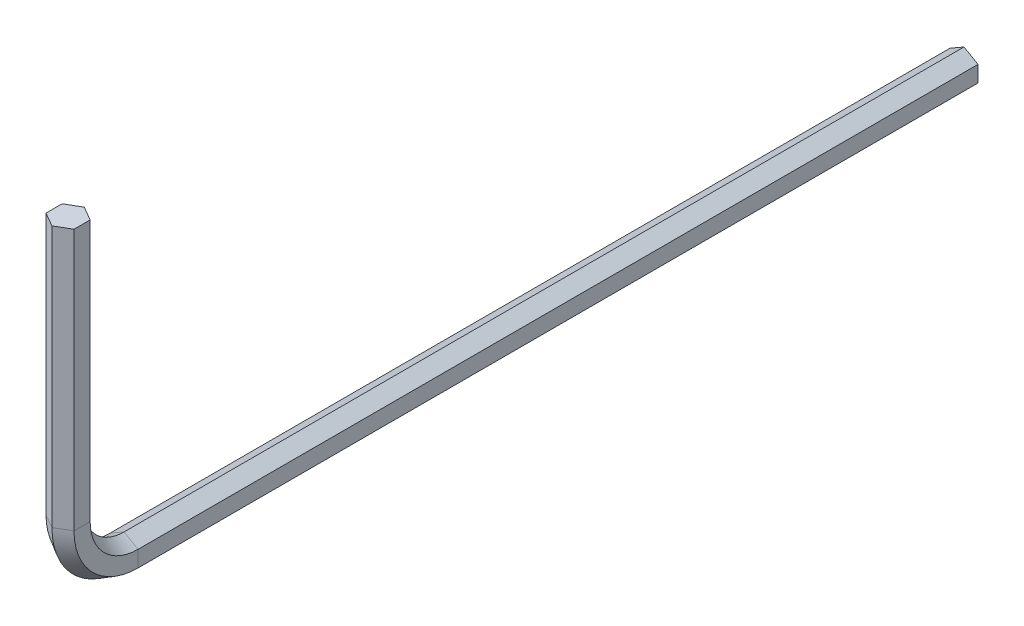
SolidWorks part; units mm, degrees
ref_plane "Front Plane" through (0, 0, 0) normal (1, 0, 0) x (0, 1, 0)
ref_plane "Top Plane" through (0, 0, 0) normal (0, 0, 1) x (0, 1, 0)
ref_plane "Right Plane" through (0, 0, 0) normal (0, 1, 0) x (-1, 0, 0)
sketch "Sketch1" plane through (0, 0, 0) normal (0, 0, 1) x (0, 1, 0)
  line L2 (0.866, 0) -> (0.433, 0.75)
  line L3 (0.433, 0.75) -> (-0.433, 0.75)
  line L4 (-0.433, 0.75) -> (-0.866, 0)
  line L5 (-0.866, 0) -> (-0.433, -0.75)
  line L6 (-0.433, -0.75) -> (0.433, -0.75)
  line L7 (0.433, -0.75) -> (0.866, 0)
  circle A0 centre (0, 0) radius 0.75 construction
sketch3d "3DSketch1"
  line L0 (0, 0, 0) -> (0, 0, 45)
  line L1 (0, 3, 48) -> (0, 17, 48)
  arc A0 (0, 3, 48) -> (0, 0, 45) centre (0, 3, 45) ccw
  point P6 (0, 0, 48)
  point P7 (3, 3, 45)
  dimension "D1" = 3
sweep "Sweep1" add profiles "Sketch1" path "3DSketch1"
